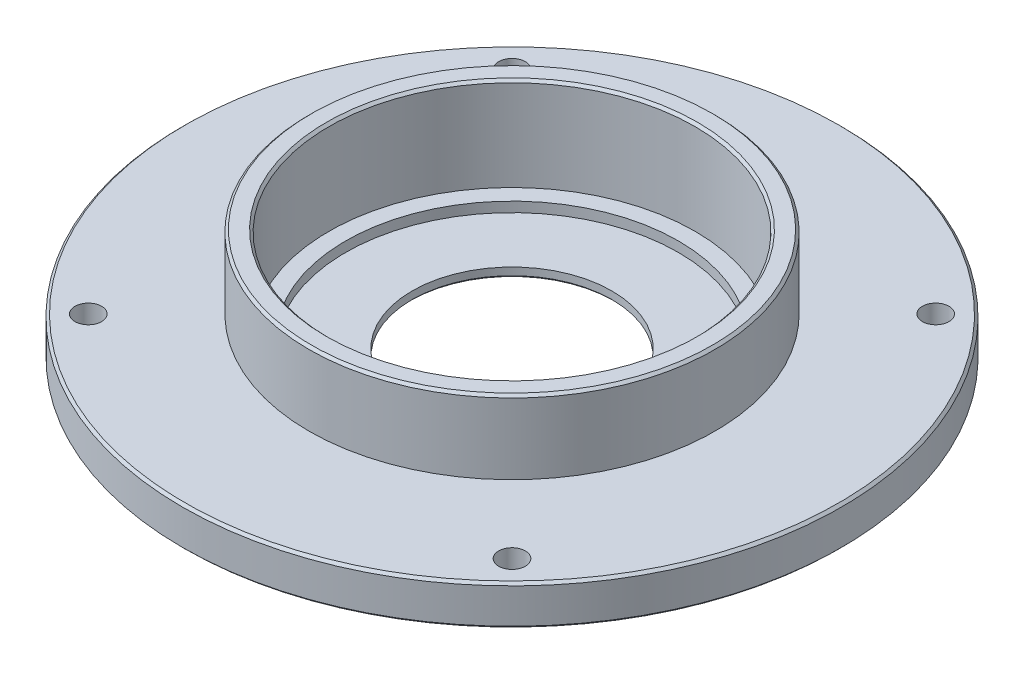
SolidWorks part; units mm, degrees
material "AISI 1045 Steel, cold drawn"
ref_plane "Front Plane" through (0, 0, 0) normal (0, 0, 1) x (1, 0, 0)
ref_plane "Top Plane" through (0, 0, 0) normal (0, 1, 0) x (1, 0, 0)
ref_plane "Right Plane" through (0, 0, 0) normal (1, 0, 0) x (0, 0, -1)
sketch "Sketch1" plane through (0, 0, 0) normal (0, 0, 1) x (1, 0, 0)
  line L0 (-50, 3) -> (-50, 6)
  line L1 (-50, 6) -> (-55, 6)
  line L2 (-55, 6) -> (-55, 34)
  line L3 (-55, 34) -> (-61, 34)
  line L6 (-61, 34) -> (-61, 12)
  line L7 (-61, 12) -> (-99, 12)
  line L8 (-99, 12) -> (-99, 0)
  line L12 (0, 0) -> (0, 12.1523) construction
  line L13 (-30, 3) -> (-30, 0)
  line L14 (-30, 0) -> (-99, 0)
  line L15 (-50, 3) -> (-30, 3)
  dimension "D1" = 50
  dimension "D2" = 3
  dimension "D3" = 55
  dimension "D4" = 28
  dimension "D5" = 3
  dimension "D6" = 6
  dimension "D7" = 99
  dimension "D8" = 30
  dimension "D9" = 12
revolve "Revolve2" add sketch "Sketch1" angle 360 about L12
sketch "Sketch2" plane through (0, 12, 0) normal (0, 1, 0) x (1, 0, 0)
  line L1 (-63.6396, -63.6396) -> (63.6396, -63.6396) construction
  line L2 (-63.6396, -63.6396) -> (-63.6396, 63.6396) construction
  line L3 (-63.6396, 63.6396) -> (63.6396, 63.6396) construction
  line L4 (63.6396, -63.6396) -> (63.6396, 63.6396) construction
  line L5 (-63.6396, -63.6396) -> (63.6396, 63.6396) construction
  line L6 (-63.6396, 63.6396) -> (63.6396, -63.6396) construction
  circle A0 centre (-63.6396, 63.6396) radius 4
  circle A1 centre (63.6396, 63.6396) radius 4
  circle A2 centre (63.6396, -63.6396) radius 4
  circle A3 centre (-63.6396, -63.6396) radius 4
  circle A4 centre (0, 0) radius 80 construction
  point P0 (0, 0)
  dimension "D2" = 8
  dimension "D3" = 160
  dimension "D1" = 180
extrude "Cut-Extrude1" cut sketch "Sketch2" against normal up to next
chamfer "Chamfer1" distance 0.75 angle 45 5 edges at (0, 12, -99) (0, 34, -55) (0, 34, -61) (0, 0, -30) (0, 0, -99)
